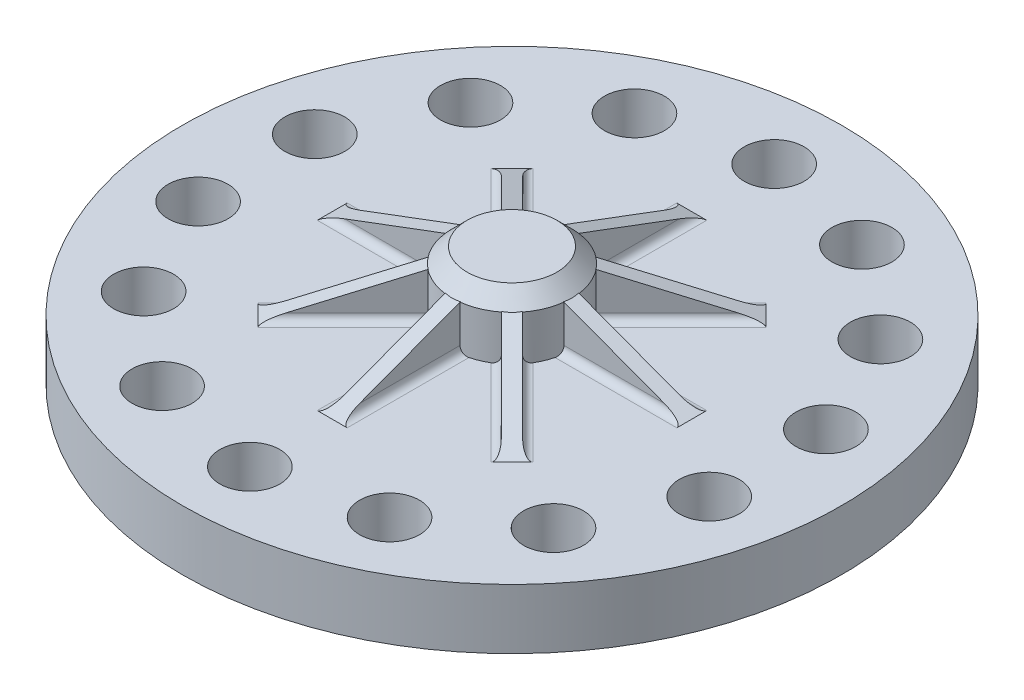
SolidWorks part; units mm, degrees
ref_plane "Front Plane" through (0, 0, 0) normal (0, 0, 1) x (1, 0, 0)
ref_plane "Top Plane" through (0, 0, 0) normal (0, 1, 0) x (1, 0, 0)
ref_plane "Right Plane" through (0, 0, 0) normal (1, 0, 0) x (0, 0, -1)
sketch "Sketch3" plane through (0, 0, 0) normal (0, 0, 1) x (1, 0, 0)
  line L0 (0, 0) -> (0, 25.4) construction
  line L1 (0, 25.4) -> (9.525, 25.4)
  line L2 (9.525, 25.4) -> (12.7, 22.225)
  line L3 (12.7, 22.225) -> (12.7, 12.7)
  line L4 (12.7, 12.7) -> (69.85, 12.7)
  line L5 (69.85, 12.7) -> (69.85, 0)
  line L6 (69.85, 0) -> (0, 0)
  line L7 (0, 0) -> (0, 25.4)
  point P5 (12.7, 25.4)
  dimension "D1" = 25.4
  dimension "D2" = 69.85
  dimension "D3" = 12.7
  dimension "D4" = 12.7
revolve "Revolve1" add sketch "Sketch3" angle 360 about L0
sketch "Sketch4" plane through (0, 12.7, 0) normal (0, 1, 0) x (1, 0, 0)
  circle A0 centre (0, 0) radius 55.5625 construction
  circle A1 centre (0, 55.5625) radius 6.35
  circle A2 centre (24.1077, 50.0601) radius 6.35
  circle A3 centre (43.4405, 34.6427) radius 6.35
  circle A4 centre (54.1694, 12.3638) radius 6.35
  circle A5 centre (54.1694, -12.3638) radius 6.35
  circle A6 centre (43.4405, -34.6427) radius 6.35
  circle A7 centre (24.1077, -50.0601) radius 6.35
  circle A8 centre (0, -55.5625) radius 6.35
  circle A9 centre (-24.1077, -50.0601) radius 6.35
  circle A10 centre (-43.4405, -34.6427) radius 6.35
  circle A11 centre (-54.1694, -12.3638) radius 6.35
  circle A12 centre (-54.1694, 12.3638) radius 6.35
  circle A13 centre (-43.4405, 34.6427) radius 6.35
  circle A14 centre (-24.1077, 50.0601) radius 6.35
  point P33 (0, 0)
  dimension "D1" = 111.125
  dimension "D2" = 12.7
  dimension "D3" = 14
extrude "Cut-Extrude1" cut sketch "Sketch4" against normal through all
sketch "Sketch6" plane through (0, 0, 0) normal (1, 0, 0) x (0, 0, -1)
  line L0 (12.7, 22.225) -> (38.1, 12.7)
  line L1 (69.85, 12.7) -> (-69.85, 12.7) construction
  dimension "D1" = 38.1
rib "Rib9" sketch "Sketch6" sketch "Sketch6" thickness 3.175 extrusion direction parallel to sketch draft on no parameters "D1"=3.175
fillet "Fillet1" radius 1.5875 2 edges at (-1.5875, 12.7, -25.3502) (1.5875, 12.7, -25.3502)
pattern_circular "CirPattern1" count 8 over 360 about axis through (0, 0, 0) along (0, 1, 0) of "Fillet1", "Rib9"
sketch "Sketch7" plane through (0, 12.7, 0) normal (0, 1, 0) x (1, 0, 0)
  point P0 (-54.1694, -12.3638)
  point P1 (-54.1694, 12.3638)
  point P5 (-43.4405, 34.6427)
  point P6 (-24.1077, 50.0601)
  point P7 (0, 55.5625)
  point P8 (24.1077, 50.0601)
  point P9 (43.4405, 34.6427)
  point P10 (54.1694, 12.3638)
  point P11 (54.1694, -12.3638)
  point P12 (43.4405, -34.6427)
  point P13 (24.1077, -50.0601)
  point P14 (0, -55.5625)
  point P15 (-24.1077, -50.0601)
  point P16 (-43.4405, -34.6427)
  point P17 (0, 0)
  dimension "D1" = 14
